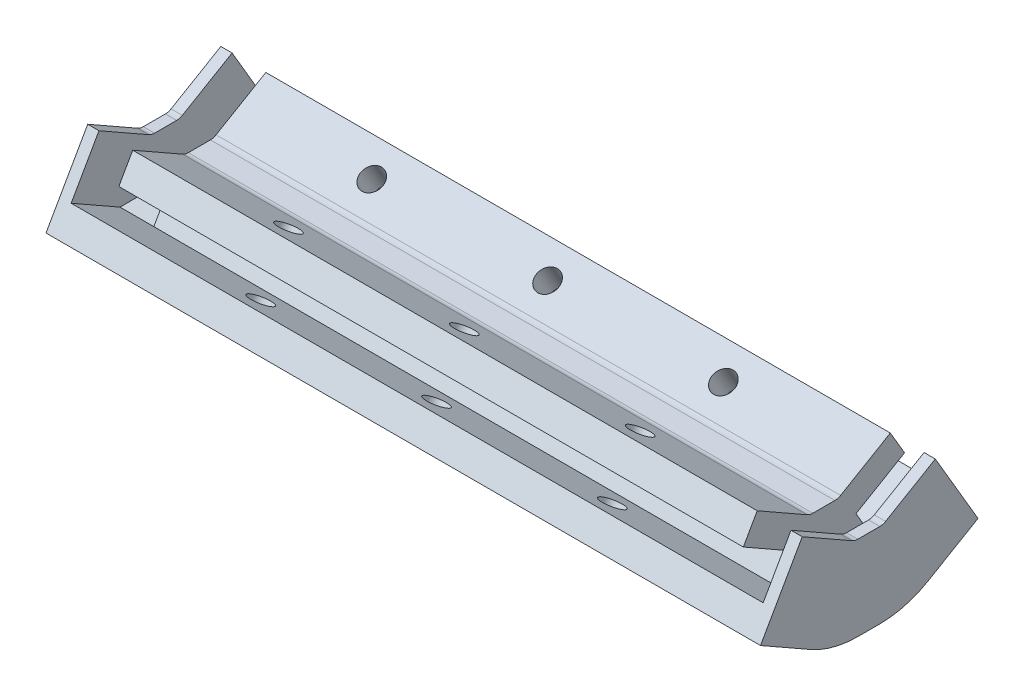
SolidWorks part; units mm, degrees
ref_plane "Alzado" through (0, 0, 0) normal (0, 0, 1) x (1, 0, 0)
ref_plane "Planta" through (0, 0, 0) normal (0, 1, 0) x (1, 0, 0)
ref_plane "Vista lateral" through (0, 0, 0) normal (1, 0, 0) x (0, 0, -1)
sketch "Croquis1" plane through (0, 0, 0) normal (1, 0, 0) x (0, 0, -1)
  line L0 (-2.2041, 4.7678) -> (2.336, 2.1853)
  line L1 (8.2642, 2.1982) -> (12.7959, 4.8536)
  line L2 (3.3249, 1.9238) -> (7.2531, 1.9238)
  line L3 (-7.1482, -3.9245) -> (-2.6081, -6.507)
  line L4 (3.3249, -8.0762) -> (7.2531, -8.0762)
  line L5 (13.3199, -6.4296) -> (17.8515, -3.7742)
  line L6 (-9.6203, -8.2707) -> (-2.2041, 4.7678)
  line L7 (12.7959, 4.8536) -> (20.3794, -8.0882)
  line L8 (15.8477, -10.7436) -> (20.3794, -8.0882)
  line L9 (-9.6203, -8.2707) -> (-5.0801, -10.8531)
  line L10 (3.3249, -13.0762) -> (7.2531, -13.0762)
  arc A0 (7.2531, 1.9238) -> (8.2642, 2.1982) centre (7.2531, 3.9238) ccw
  arc A1 (3.3249, 1.9238) -> (2.336, 2.1853) centre (3.3249, 3.9238) cw
  arc A2 (3.3249, -8.0762) -> (-2.6081, -6.507) centre (3.3249, 3.9238) cw
  arc A3 (7.2531, -8.0762) -> (13.3199, -6.4296) centre (7.2531, 3.9238) ccw
  arc A4 (3.3249, -13.0762) -> (-5.0801, -10.8531) centre (3.3249, 3.9238) cw
  arc A5 (7.2531, -13.0762) -> (15.8477, -10.7436) centre (7.2531, 3.9238) ccw
  point P7 (7.7959, 1.9238)
  point P10 (2.7959, 1.9238)
  dimension "D4" = 2
  dimension "D1" = 15
  dimension "D2" = 5
  dimension "D3" = 5
  dimension "D5" = 120
  dimension "D6" = 10
  dimension "D7" = 10
  dimension "D8" = 5
extrude "Saliente-Extruir1" add sketch "Croquis1" along normal blind 111 contours L4 A3 L5 L7 L1 A0 L2 A1 L0 L6 L3 A2 | L10 A5 L8 L7 L5 A3 L4 A2 L3 L6 L9 A4
sketch "Croquis2" plane through (0, 6.8221, -11.6424) normal (0, 0.5056, -0.8628) x (1, 0, 0)
  line L0 (0, 9.7815) -> (111, 9.7815) construction
  line L1 (0, 2.2815) -> (0, 17.2815) construction
  line L2 (111, 2.2815) -> (111, 17.2815) construction
  line L4 (0, 12.2815) -> (111, 12.2815)
  line L5 (0, 12.2815) -> (0, 7.2815)
  line L6 (0, 7.2815) -> (111, 7.2815)
  line L7 (111, 12.2815) -> (111, 7.2815)
  dimension "D1" = 2.5
  dimension "D2" = 2.5
extrude "Cortar-Extruir1" cut sketch "Croquis2" against normal blind 5
sketch "Croquis3" plane through (0, 2.1127, 3.7143) normal (0, 0.4944, 0.8692) x (1, 0, 0)
  line L0 (0, -4.4455) -> (111, -4.4455) construction
  line L1 (0, -11.9455) -> (0, 3.0545) construction
  line L2 (111, -11.9455) -> (111, 3.0545) construction
  line L4 (0, -1.9455) -> (111, -1.9455)
  line L5 (0, -1.9455) -> (0, -6.9455)
  line L6 (0, -6.9455) -> (111, -6.9455)
  line L7 (111, -1.9455) -> (111, -6.9455)
  dimension "D1" = 2.5
  dimension "D2" = 2.5
extrude "Cortar-Extruir2" cut sketch "Croquis3" against normal blind 5
sketch "Croquis8" plane through (0, 2.1127, 3.7143) normal (0, 0.4944, 0.8692) x (1, 0, 0)
  line L4 (0, -1.9455) -> (111, -1.9455)
  line L5 (111, -1.9455) -> (111, 3.0545)
  line L6 (111, 3.0545) -> (0, 3.0545)
  line L7 (0, 3.0545) -> (0, -1.9455)
  line L8 (0, -1.9455) -> (111, -1.9455)
  line L9 (111, -1.9455) -> (111, 3.0545)
  line L10 (111, 3.0545) -> (0, 3.0545)
  line L11 (0, 3.0545) -> (0, -1.9455)
  dimension "D1" = 0
extrude "Saliente-Extruir6" add sketch "Croquis8" along normal blind 5
sketch "Croquis9" plane through (0, 2.1127, 3.7143) normal (0, 0.4944, 0.8692) x (1, 0, 0)
  line L4 (111, -6.9455) -> (0, -6.9455)
  line L5 (0, -6.9455) -> (0, -11.9455)
  line L6 (0, -11.9455) -> (111, -11.9455)
  line L7 (111, -11.9455) -> (111, -6.9455)
  line L8 (111, -6.9455) -> (0, -6.9455)
  line L9 (0, -6.9455) -> (0, -11.9455)
  line L11 (111, -11.9455) -> (111, -6.9455)
  line L12 (0, -11.9455) -> (111, -11.9455)
  dimension "D1" = 0
extrude "Saliente-Extruir7" add sketch "Croquis9" along normal blind 5
sketch "Croquis10" plane through (0, 6.8221, -11.6424) normal (0, 0.5056, -0.8628) x (-1, 0, 0)
  line L4 (-111, -7.2815) -> (0, -7.2815)
  line L5 (0, -7.2815) -> (0, -2.2815)
  line L6 (0, -2.2815) -> (-111, -2.2815)
  line L7 (-111, -2.2815) -> (-111, -7.2815)
  line L8 (-111, -7.2815) -> (0, -7.2815)
  line L9 (0, -7.2815) -> (0, -2.2815)
  line L10 (0, -2.2815) -> (-111, -2.2815)
  line L11 (-111, -2.2815) -> (-111, -7.2815)
  dimension "D1" = 0
extrude "Saliente-Extruir8" add sketch "Croquis10" along normal blind 5
sketch "Croquis11" plane through (0, 6.8221, -11.6424) normal (0, 0.5056, -0.8628) x (-1, 0, 0)
  line L4 (0, -12.2815) -> (-111, -12.2815)
  line L5 (-111, -12.2815) -> (-111, -17.2815)
  line L6 (-111, -17.2815) -> (0, -17.2815)
  line L7 (0, -17.2815) -> (0, -12.2815)
  line L8 (0, -12.2815) -> (-111, -12.2815)
  line L9 (-111, -12.2815) -> (-111, -17.2815)
  line L11 (0, -17.2815) -> (0, -12.2815)
  line L12 (-111, -17.2815) -> (0, -17.2815)
  dimension "D1" = 0
extrude "Saliente-Extruir9" add sketch "Croquis11" along normal blind 5
sketch "Croquis4" plane through (0, 0, 0) normal (-1, 0, 0) x (0, 0, 1)
  line L0 (-13.5376, -6.3021) -> (2.8021, -6.3966)
  line L16 (2.8021, -6.3966) -> (0.33, -2.0504)
  line L17 (0.33, -2.0504) -> (9.0223, 2.8937)
  line L18 (9.0223, 2.8937) -> (6.5503, 7.2398)
  line L19 (6.5503, 7.2398) -> (-2.336, 2.1853)
  line L20 (-3.3249, 1.9238) -> (-7.2531, 1.9238)
  line L21 (-8.2642, 2.1982) -> (-17.1098, 7.3815)
  line L22 (9.0223, 2.8937) -> (6.5503, 7.2398)
  line L23 (-19.6376, 3.0676) -> (-11.0098, -1.9881)
  line L24 (-11.0098, -1.9881) -> (-13.5376, -6.3021)
  line L25 (-13.5376, -6.3021) -> (-22.1655, -1.2464)
  line L26 (-17.1098, 7.3815) -> (-19.6376, 3.0676)
  line L27 (-24.6933, -5.5603) -> (-15.8477, -10.7436)
  line L28 (-24.6933, -5.5603) -> (-15.8477, -10.7436)
  line L29 (-7.2531, -13.0762) -> (-3.3249, -13.0762)
  line L30 (-17.1098, 7.3815) -> (-19.6376, 3.0676)
  line L31 (11.4944, -1.4525) -> (2.8021, -6.3966)
  line L32 (2.8021, -6.3966) -> (0.33, -2.0504)
  line L33 (0.33, -2.0504) -> (9.0223, 2.8937)
  line L35 (6.5503, 7.2398) -> (-2.336, 2.1853)
  line L36 (-3.3249, 1.9238) -> (-7.2531, 1.9238)
  line L37 (-8.2642, 2.1982) -> (-17.1098, 7.3815)
  line L39 (-19.6376, 3.0676) -> (-11.0098, -1.9881)
  line L40 (-11.0098, -1.9881) -> (-13.5376, -6.3021)
  line L41 (-13.5376, -6.3021) -> (-22.1655, -1.2464)
  line L47 (11.4944, -1.4525) -> (2.8021, -6.3966)
  line L49 (-22.1655, -1.2464) -> (-24.6933, -5.5603)
  line L50 (-22.1655, -1.2464) -> (-24.6933, -5.5603)
  line L51 (13.9664, -5.7986) -> (11.4944, -1.4525)
  line L52 (13.9664, -5.7986) -> (11.4944, -1.4525)
  line L53 (-7.2531, -13.0762) -> (-3.3249, -13.0762)
  line L54 (5.0801, -10.8531) -> (13.9664, -5.7986)
  line L55 (5.0801, -10.8531) -> (13.9664, -5.7986)
  arc A4 (-3.3249, 1.9238) -> (-2.336, 2.1853) centre (-3.3249, 3.9238) ccw
  arc A5 (-8.2642, 2.1982) -> (-7.2531, 1.9238) centre (-7.2531, 3.9238) ccw
  arc A6 (-15.8477, -10.7436) -> (-7.2531, -13.0762) centre (-7.2531, 3.9238) ccw
  arc A7 (-15.8477, -10.7436) -> (-7.2531, -13.0762) centre (-7.2531, 3.9238) ccw
  arc A8 (-3.3249, 1.9238) -> (-2.336, 2.1853) centre (-3.3249, 3.9238) ccw
  arc A9 (-8.2642, 2.1982) -> (-7.2531, 1.9238) centre (-7.2531, 3.9238) ccw
  arc A12 (-3.3249, -13.0762) -> (5.0801, -10.8531) centre (-3.3249, 3.9238) ccw
  arc A13 (-3.3249, -13.0762) -> (5.0801, -10.8531) centre (-3.3249, 3.9238) ccw
  dimension "D1" = 0
extrude "Saliente-Extruir2" add sketch "Croquis4" along normal blind 8
sketch "Croquis5" plane through (-8, 0, 0) normal (-1, 0, 0) x (0, 0, 1)
  line L1 (-17.1098, 7.3815) -> (-22.1655, -1.2464)
  line L5 (6.5503, 7.2398) -> (-2.336, 2.1853) construction
  line L6 (-3.3249, 1.9238) -> (-7.2531, 1.9238) construction
  line L7 (-8.2642, 2.1982) -> (-17.1098, 7.3815) construction
  line L8 (6.5503, 7.2398) -> (11.4944, -1.4525)
  line L23 (6.5503, 7.2398) -> (-2.336, 2.1853)
  line L24 (-3.3249, 1.9238) -> (-7.2531, 1.9238)
  line L25 (-8.2642, 2.1982) -> (-17.1098, 7.3815)
  line L43 (2.8021, -6.3966) -> (-13.5376, -6.3021)
  line L44 (-13.5376, -6.3021) -> (-22.1655, -1.2464)
  line L45 (-22.1655, -1.2464) -> (-24.6933, -5.5603)
  line L46 (-24.6933, -5.5603) -> (-15.8477, -10.7436)
  line L47 (-7.2531, -13.0762) -> (-3.3249, -13.0762)
  line L48 (5.0801, -10.8531) -> (13.9664, -5.7986)
  line L49 (13.9664, -5.7986) -> (11.4944, -1.4525)
  line L50 (11.4944, -1.4525) -> (2.8021, -6.3966)
  line L51 (2.8021, -6.3966) -> (-13.5376, -6.3021)
  line L53 (-22.1655, -1.2464) -> (-24.6933, -5.5603)
  line L54 (-24.6933, -5.5603) -> (-15.8477, -10.7436)
  line L55 (-7.2531, -13.0762) -> (-3.3249, -13.0762)
  line L56 (5.0801, -10.8531) -> (13.9664, -5.7986)
  line L57 (13.9664, -5.7986) -> (11.4944, -1.4525)
  line L58 (11.4944, -1.4525) -> (2.8021, -6.3966)
  arc A0 (-3.3249, 1.9238) -> (-2.336, 2.1853) centre (-3.3249, 3.9238) ccw construction
  arc A1 (-8.2642, 2.1982) -> (-7.2531, 1.9238) centre (-7.2531, 3.9238) ccw construction
  arc A4 (-3.3249, 1.9238) -> (-2.336, 2.1853) centre (-3.3249, 3.9238) ccw
  arc A5 (-8.2642, 2.1982) -> (-7.2531, 1.9238) centre (-7.2531, 3.9238) ccw
  arc A10 (-15.8477, -10.7436) -> (-7.2531, -13.0762) centre (-7.2531, 3.9238) ccw
  arc A11 (-3.3249, -13.0762) -> (5.0801, -10.8531) centre (-3.3249, 3.9238) ccw
  arc A12 (-15.8477, -10.7436) -> (-7.2531, -13.0762) centre (-7.2531, 3.9238) ccw
  arc A13 (-3.3249, -13.0762) -> (5.0801, -10.8531) centre (-3.3249, 3.9238) ccw
  dimension "D1" = 0
extrude "Saliente-Extruir3" add sketch "Croquis5" against normal blind 2
sketch "Croquis6" plane through (111, 0, 0) normal (1, 0, 0) x (0, 0, -1)
  line L0 (-2.8021, -6.3966) -> (13.5376, -6.3021)
  line L16 (-9.0223, 2.8937) -> (-0.33, -2.0504)
  line L17 (-0.33, -2.0504) -> (-2.8021, -6.3966)
  line L18 (-2.8021, -6.3966) -> (-11.4944, -1.4525)
  line L19 (-11.4944, -1.4525) -> (-13.9664, -5.7986)
  line L20 (-13.9664, -5.7986) -> (-5.0801, -10.8531)
  line L21 (-13.9664, -5.7986) -> (-5.0801, -10.8531)
  line L22 (3.3249, -13.0762) -> (7.2531, -13.0762)
  line L23 (-11.4944, -1.4525) -> (-13.9664, -5.7986)
  line L24 (22.1655, -1.2464) -> (13.5376, -6.3021)
  line L25 (13.5376, -6.3021) -> (11.0098, -1.9881)
  line L26 (11.0098, -1.9881) -> (19.6376, 3.0676)
  line L27 (24.6933, -5.5603) -> (22.1655, -1.2464)
  line L28 (17.1098, 7.3815) -> (8.2642, 2.1982)
  line L29 (7.2531, 1.9238) -> (3.3249, 1.9238)
  line L30 (2.336, 2.1853) -> (-6.5503, 7.2398)
  line L31 (24.6933, -5.5603) -> (22.1655, -1.2464)
  line L32 (-9.0223, 2.8937) -> (-0.33, -2.0504)
  line L33 (-0.33, -2.0504) -> (-2.8021, -6.3966)
  line L34 (-2.8021, -6.3966) -> (-11.4944, -1.4525)
  line L40 (22.1655, -1.2464) -> (13.5376, -6.3021)
  line L41 (13.5376, -6.3021) -> (11.0098, -1.9881)
  line L42 (11.0098, -1.9881) -> (19.6376, 3.0676)
  line L44 (17.1098, 7.3815) -> (8.2642, 2.1982)
  line L45 (7.2531, 1.9238) -> (3.3249, 1.9238)
  line L46 (2.336, 2.1853) -> (-6.5503, 7.2398)
  line L49 (19.6376, 3.0676) -> (17.1098, 7.3815)
  line L50 (19.6376, 3.0676) -> (17.1098, 7.3815)
  line L51 (-6.5503, 7.2398) -> (-9.0223, 2.8937)
  line L52 (-6.5503, 7.2398) -> (-9.0223, 2.8937)
  line L53 (3.3249, -13.0762) -> (7.2531, -13.0762)
  line L54 (15.8477, -10.7436) -> (24.6933, -5.5603)
  line L55 (15.8477, -10.7436) -> (24.6933, -5.5603)
  arc A4 (-5.0801, -10.8531) -> (3.3249, -13.0762) centre (3.3249, 3.9238) ccw
  arc A5 (-5.0801, -10.8531) -> (3.3249, -13.0762) centre (3.3249, 3.9238) ccw
  arc A6 (7.2531, 1.9238) -> (8.2642, 2.1982) centre (7.2531, 3.9238) ccw
  arc A7 (2.336, 2.1853) -> (3.3249, 1.9238) centre (3.3249, 3.9238) ccw
  arc A10 (7.2531, 1.9238) -> (8.2642, 2.1982) centre (7.2531, 3.9238) ccw
  arc A11 (2.336, 2.1853) -> (3.3249, 1.9238) centre (3.3249, 3.9238) ccw
  arc A12 (7.2531, -13.0762) -> (15.8477, -10.7436) centre (7.2531, 3.9238) ccw
  arc A13 (7.2531, -13.0762) -> (15.8477, -10.7436) centre (7.2531, 3.9238) ccw
  dimension "D1" = 0
extrude "Saliente-Extruir4" add sketch "Croquis6" along normal blind 8
sketch "Croquis7" plane through (119, 0, 0) normal (1, 0, 0) x (0, 0, -1)
  line L5 (17.1098, 7.3815) -> (8.2642, 2.1982) construction
  line L6 (7.2531, 1.9238) -> (3.3249, 1.9238) construction
  line L7 (2.336, 2.1853) -> (-6.5503, 7.2398) construction
  line L23 (17.1098, 7.3815) -> (8.2642, 2.1982)
  line L24 (7.2531, 1.9238) -> (3.3249, 1.9238)
  line L25 (2.336, 2.1853) -> (-6.5503, 7.2398)
  line L36 (-6.5503, 7.2398) -> (-11.4944, -1.4525)
  line L37 (17.1098, 7.3815) -> (22.1655, -1.2464)
  line L46 (13.5376, -6.3021) -> (-2.8021, -6.3966)
  line L47 (-2.8021, -6.3966) -> (-11.4944, -1.4525)
  line L48 (-11.4944, -1.4525) -> (-13.9664, -5.7986)
  line L49 (-13.9664, -5.7986) -> (-5.0801, -10.8531)
  line L50 (3.3249, -13.0762) -> (7.2531, -13.0762)
  line L51 (15.8477, -10.7436) -> (24.6933, -5.5603)
  line L52 (24.6933, -5.5603) -> (22.1655, -1.2464)
  line L53 (22.1655, -1.2464) -> (13.5376, -6.3021)
  line L56 (-11.4944, -1.4525) -> (-13.9664, -5.7986)
  line L57 (-13.9664, -5.7986) -> (-5.0801, -10.8531)
  line L58 (3.3249, -13.0762) -> (7.2531, -13.0762)
  line L59 (15.8477, -10.7436) -> (24.6933, -5.5603)
  line L60 (24.6933, -5.5603) -> (22.1655, -1.2464)
  arc A0 (7.2531, 1.9238) -> (8.2642, 2.1982) centre (7.2531, 3.9238) ccw construction
  arc A1 (2.336, 2.1853) -> (3.3249, 1.9238) centre (3.3249, 3.9238) ccw construction
  arc A4 (7.2531, 1.9238) -> (8.2642, 2.1982) centre (7.2531, 3.9238) ccw
  arc A5 (2.336, 2.1853) -> (3.3249, 1.9238) centre (3.3249, 3.9238) ccw
  arc A10 (-5.0801, -10.8531) -> (3.3249, -13.0762) centre (3.3249, 3.9238) ccw
  arc A11 (7.2531, -13.0762) -> (15.8477, -10.7436) centre (7.2531, 3.9238) ccw
  arc A12 (-5.0801, -10.8531) -> (3.3249, -13.0762) centre (3.3249, 3.9238) ccw
  arc A13 (7.2531, -13.0762) -> (15.8477, -10.7436) centre (7.2531, 3.9238) ccw
  dimension "D1" = 0
extrude "Saliente-Extruir5" add sketch "Croquis7" against normal blind 2
sketch "Croquis12" plane through (0, -10.3834, 5.906) normal (0, -0.8692, 0.4944) x (-1, 0, 0)
  line L0 (8, -4.1615) -> (-119, -4.1615) construction
  line L4 (8, 0.9501) -> (8, -9.2731) construction
  line L5 (-119, -9.2731) -> (-119, 0.9501) construction
  circle A0 centre (-23.25, -4.1615) radius 2
  circle A1 centre (-54.5, -4.1615) radius 2
  circle A2 centre (-85.75, -4.1615) radius 2
  dimension "D1" = 4
  dimension "D3" = 4
  dimension "D4" = 4
  dimension "D2" = 31.25
  dimension "D5" = 31.25
  dimension "D6" = 31.25
extrude "Cortar-Extruir3" cut sketch "Croquis12" against normal blind 16
sketch "Croquis13" plane through (0, -10.3834, 5.906) normal (0, -0.8692, 0.4944) x (1, 0, 0)
  circle A0 centre (23.25, 4.1615) radius 4
  circle A1 centre (54.5, 4.1615) radius 4
  circle A2 centre (85.75, 4.1615) radius 4
  dimension "D1" = 8
extrude "Cortar-Extruir4" cut sketch "Croquis13" against normal blind 4
sketch "Croquis14" plane through (0, -14.9103, -8.737) normal (0, -0.8628, -0.5056) x (-1, 0, 0)
  line L0 (8, 13.3678) -> (-119, 13.3678) construction
  line L1 (8, 18.494) -> (8, 8.2416) construction
  line L2 (-119, 8.2416) -> (-119, 18.494) construction
  circle A0 centre (-23.25, 13.3678) radius 2
  circle A1 centre (-54.5, 13.3678) radius 2
  circle A2 centre (-85.75, 13.3678) radius 2
  dimension "D1" = 4
  dimension "D2" = 31.25
  dimension "D3" = 31.25
  dimension "D4" = 31.25
extrude "Cortar-Extruir5" cut sketch "Croquis14" against normal blind 16
sketch "Croquis15" plane through (0, -14.9103, -8.737) normal (0, -0.8628, -0.5056) x (1, 0, 0)
  circle A0 centre (23.25, -13.3678) radius 4
  circle A1 centre (54.5, -13.3678) radius 4
  circle A2 centre (85.75, -13.3678) radius 4
  dimension "D1" = 8
extrude "Cortar-Extruir6" cut sketch "Croquis15" against normal blind 4
